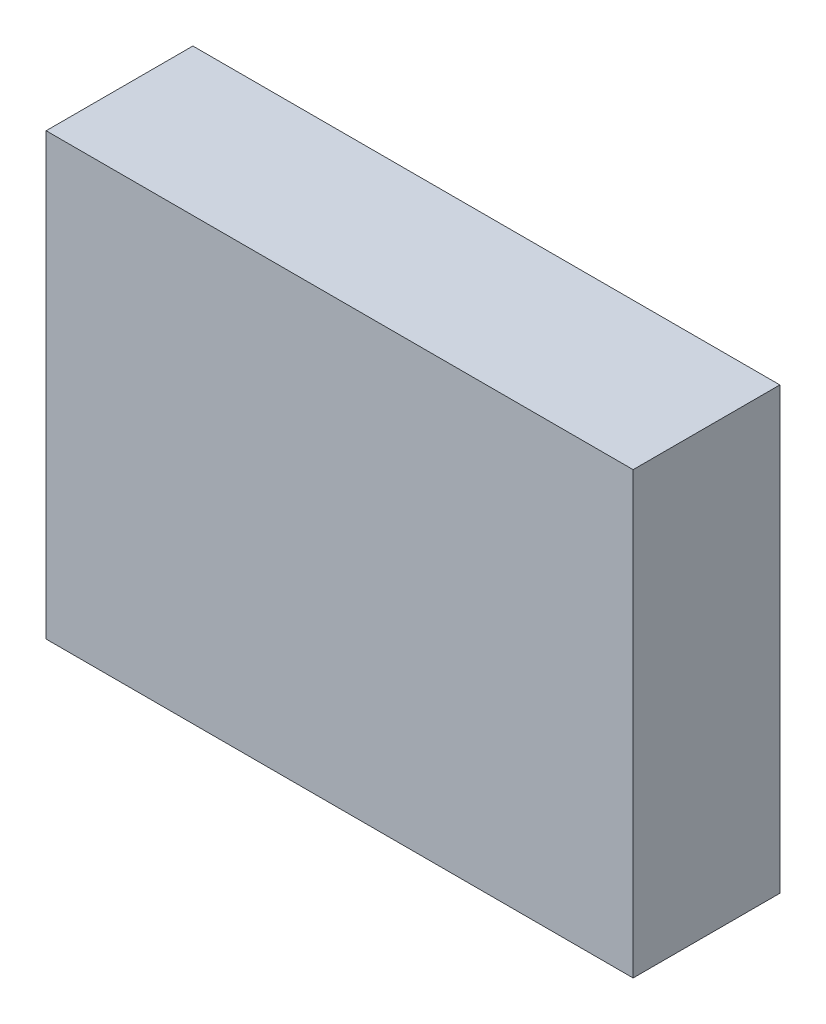
SolidWorks part; units mm, degrees
material "Plain Carbon Steel"
ref_plane "Front Plane" through (0, 0, 0) normal (0, 0, 1) x (1, 0, 0)
ref_plane "Top Plane" through (0, 0, 0) normal (0, 1, 0) x (1, 0, 0)
ref_plane "Right Plane" through (0, 0, 0) normal (1, 0, 0) x (0, 0, -1)
sketch "Sketch1" plane through (0, 0, 0) normal (0, 0, 1) x (1, 0, 0)
  line L0 (-20, 0) -> (20, 0)
  line L1 (-20, 0) -> (-20, 30)
  line L2 (20, 0) -> (20, 30)
  line L3 (-20, 30) -> (20, 30)
  line L4 (-20, 0) -> (20, 30) construction
  line L5 (20, 0) -> (-20, 30) construction
  line L6 (0, 0) -> (0, 83.8898) construction
  point P1 (0, 15)
  dimension "D1" = 30
  dimension "D2" = 40
extrude "Boss-Extrude1" add sketch "Sketch1" along normal mid plane 10
